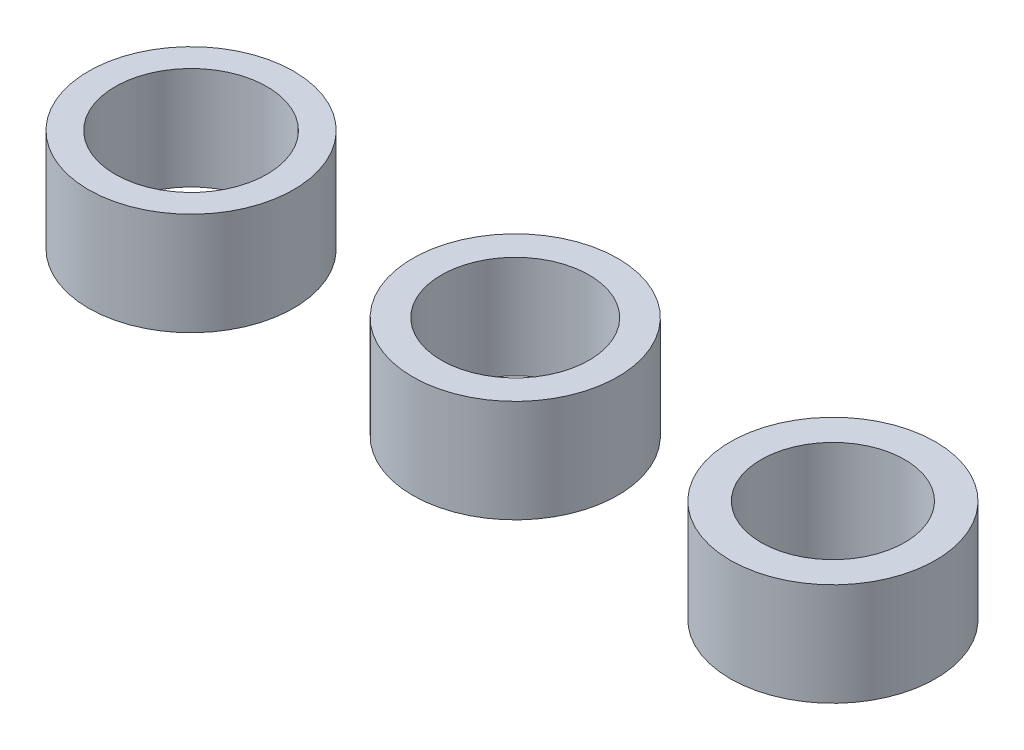
SolidWorks part; units mm, degrees
ref_plane "前视基准面" through (0, 0, 0) normal (0, 0, 1) x (1, 0, 0)
ref_plane "上视基准面" through (0, 0, 0) normal (0, 1, 0) x (1, 0, 0)
ref_plane "右视基准面" through (0, 0, 0) normal (1, 0, 0) x (0, 0, -1)
other "Configuration Table"
sketch "草图1" plane through (0, 0, 0) normal (0, 1, 0) x (1, 0, 0)
  circle A0 centre (5.4371, 5.0069) radius 3.7
  circle A1 centre (5.4371, 5.0069) radius 5
  circle A2 centre (21.2301, 5.0069) radius 3.6
  circle A3 centre (21.2301, 5.0069) radius 5
  circle A4 centre (36.708, 5.0069) radius 3.5
  circle A5 centre (36.708, 5.0069) radius 5
extrude "凸台-拉伸1" add sketch "草图1" along normal blind 5
